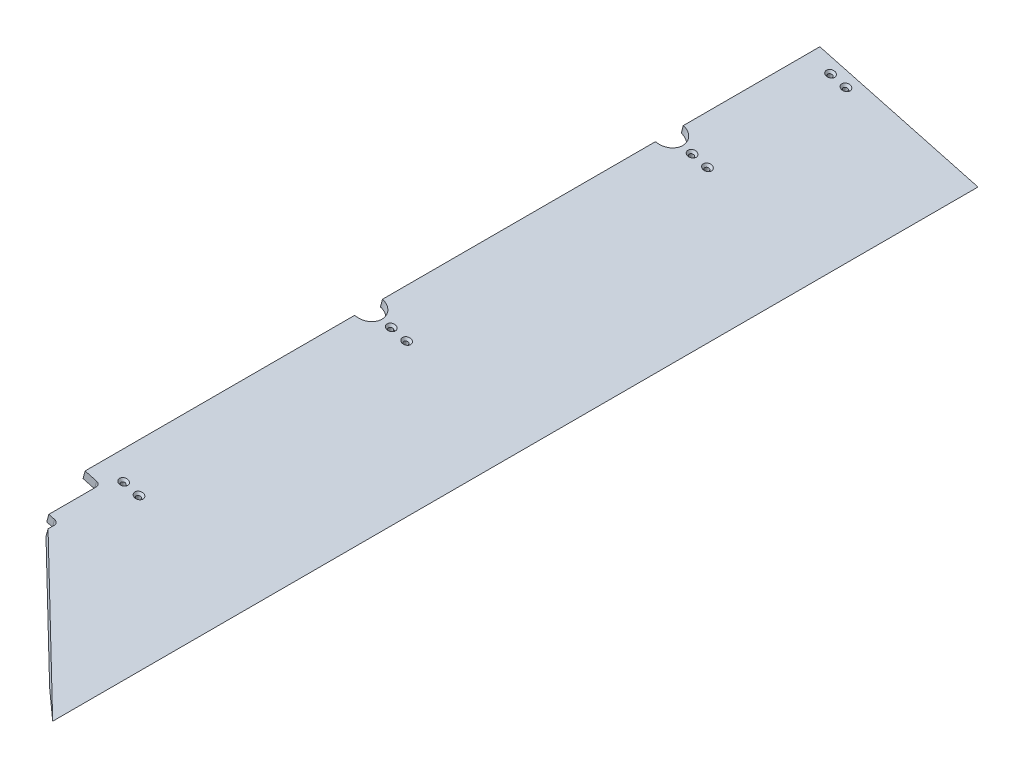
SolidWorks part; units mm, degrees
material "PE High Density"
ref_plane "Front Plane" through (0, 0, 0) normal (0, 0, 1) x (1, 0, 0)
ref_plane "Top Plane" through (0, 0, 0) normal (0, 1, 0) x (1, 0, 0)
ref_plane "Right Plane" through (0, 0, 0) normal (1, 0, 0) x (0, 0, -1)
sketch "Sketch1" plane through (0, 0, 0) normal (0, 0, 1) x (1, 0, 0)
  line L0 (0, 44.45) -> (44.45, 44.45) construction
  line L1 (0, 0) -> (44.45, 0) construction
  line L2 (0, 0) -> (0, 44.45) construction
  line L3 (0, 44.45) -> (44.45, 44.45) construction
  line L4 (44.45, 0) -> (44.45, 44.45) construction
  line L5 (45.6826, 44.2877) -> (113.7307, 26.0543) construction
  line L6 (113.7307, 26.0543) -> (114.9634, 30.6545) construction
  line L7 (114.9634, 30.6545) -> (46.9153, 48.8879) construction
  line L8 (44.45, 49.2125) -> (0, 49.2125) construction
  line L9 (0, 49.2125) -> (0, 44.45) construction
  line L10 (22.225, 55.5037) -> (229.3675, 0)
  line L11 (229.3675, 0) -> (278.4366, 0)
  line L12 (278.4366, 0) -> (25.512, 67.7709)
  line L13 (25.512, 67.7709) -> (22.225, 55.5037)
  arc A0 (45.6826, 44.2877) -> (44.45, 44.45) centre (44.45, 39.6875) ccw construction
  arc A1 (46.9153, 48.8879) -> (44.45, 49.2125) centre (44.45, 39.6875) ccw construction
  point P19 (22.225, 44.45)
  dimension "D3" = 4.7625
  dimension "D4" = 9.525
  dimension "D1" = 44.45
  dimension "D2" = 4.7625
  dimension "D5" = 44.45
  dimension "D6" = 75
  dimension "D7" = 12.7
extrude "Boss-Extrude1" add sketch "Sketch1" along normal blind 1479.55
hole_wizard "CSK for 1/4 Flat Head Socket Cap Screw1" positions "Sketch2" profile "Sketch3" countersink size "1/4" standard "ANSI Inch" end condition through all
sketch "Sketch2" plane through (18.6517, 69.6091, 0) normal (0.2588, 0.9659, 0) x (0.9659, -0.2588, 0)
  line L0 (7.1023, -1479.55) -> (7.1023, 0) construction
  line L2 (268.9491, 0) -> (7.1023, 0) construction
  point P0 (44.6689, -721.5187)
  point P2 (70.0689, -721.5187)
  point P4 (44.6689, -240.5063)
  point P6 (70.0689, -240.5063)
  point P12 (44.6689, -1149.35)
  point P14 (70.0689, -1149.35)
  point P16 (44.6689, -19.05)
  point P18 (70.0689, -19.05)
  dimension "D1" = 240.5062
  dimension "D2" = 481.0125
  dimension "D3" = 37.5666
  dimension "D4" = 25.4
  dimension "D5" = 1149.35
  dimension "D6" = 19.05
sketch "Sketch3" plane through (61.7986, 58.048, 721.5187) normal (0, 0, 1) x (-0.9659, 0.2588, 0)
  line L0 (0, 0) -> (0, 66.3124)
  line L1 (0, 66.3124) -> (3.5712, 66.3124)
  line L2 (3.5712, 66.3124) -> (3.5712, 3.6495)
  line L3 (3.5712, 3.6495) -> (6.7437, 0)
  line L5 (6.7437, 0) -> (0, 0)
  line L6 (-3.5712, 3.6495) -> (-6.7437, 0) construction
  line L11 (0, -6.35) -> (0, 107.95) construction
  dimension "Thru Hole Dia." = 7.1425
  dimension "Thru Hole Depth" = 66.3124
  dimension "Near C'Sink Dia." = 13.4874
  dimension "Near C'Sink Angle" = 82
sketch "Sketch4" plane through (18.6517, 69.6091, 0) normal (0.2588, 0.9659, 0) x (0.9659, -0.2588, 0)
  line L0 (7.1023, -1479.55) -> (7.1023, 0) construction
  line L1 (268.9491, 0) -> (7.1023, 0) construction
  circle A0 centre (7.1023, -240.5062) radius 22.225
  circle A1 centre (7.1023, -721.5187) radius 22.225
  dimension "D1" = 44.45
  dimension "D2" = 240.5062
  dimension "D3" = 481.0125
extrude "Cut-Extrude1" cut sketch "Sketch4" against normal through all
sketch "Sketch5" plane through (18.6517, 69.6091, 0) normal (0.2588, 0.9659, 0) x (0.9659, -0.2588, 0)
  line L0 (268.9491, -1479.55) -> (48.3773, -1273.8635)
  line L1 (48.3773, -1273.8635) -> (48.3773, -1257.3)
  line L2 (48.3773, -1257.3) -> (32.5023, -1257.3)
  line L3 (32.5023, -1257.3) -> (32.5023, -1174.75)
  line L4 (32.5023, -1174.75) -> (7.1023, -1174.75)
  line L5 (7.1023, -1479.55) -> (7.1023, -743.7437) construction
  line L6 (7.1023, -1174.75) -> (7.1023, -1479.55)
  line L7 (7.1023, -1479.55) -> (268.9491, -1479.55)
  line L8 (7.1023, -1479.55) -> (7.1023, -743.7437) construction
  line L9 (268.9491, 0) -> (7.1023, 0) construction
  line L10 (268.9491, -1479.55) -> (268.9491, 0) construction
  dimension "D1" = 25.4
  dimension "D2" = 1174.75
  dimension "D3" = 1257.3
  dimension "D4" = 41.275
  dimension "D5" = 47
extrude "Cut-Extrude2" cut sketch "Sketch5" against normal through all
fillet "Fillet1" radius 6.35 2 edges at (48.403, 55.0633, 1174.75) (63.7371, 50.9545, 1257.3)
